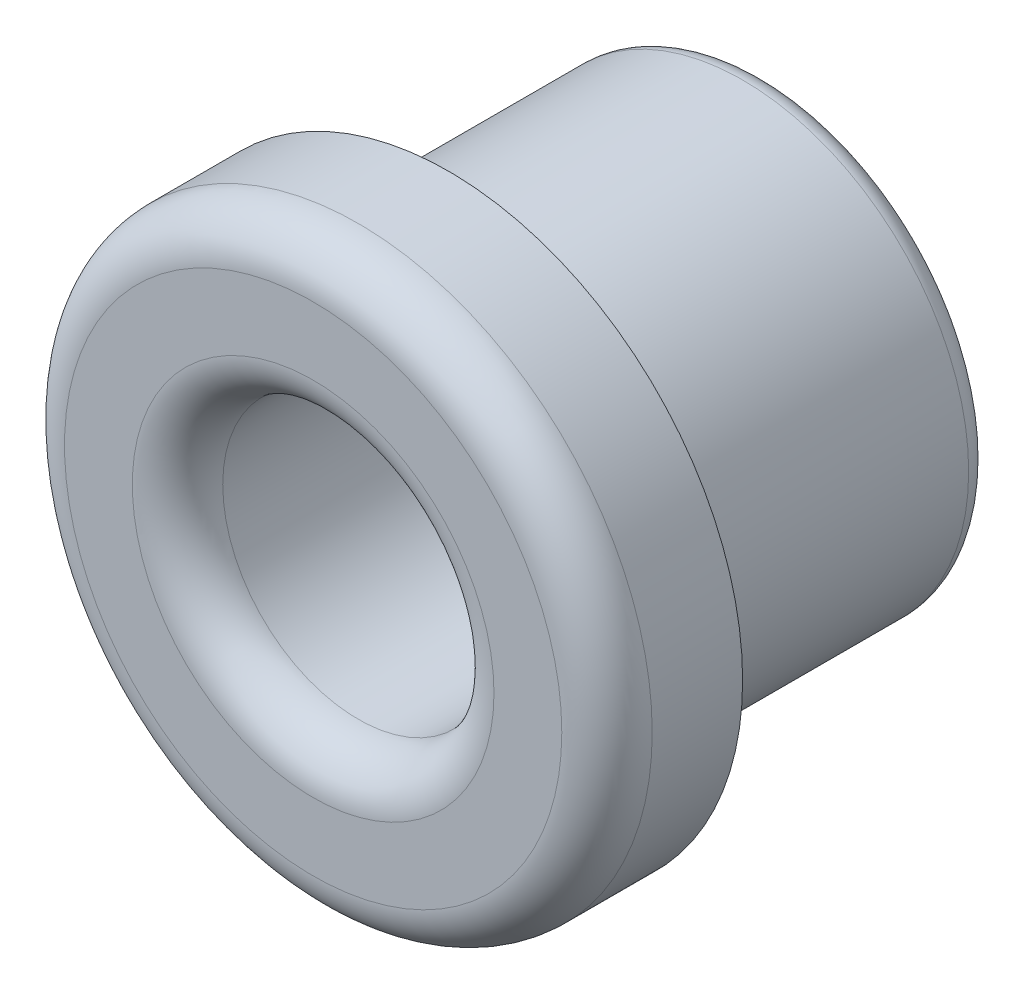
SolidWorks part; units mm, degrees
ref_plane "Front Plane" through (0, 0, 0) normal (0, 0, 1) x (1, 0, 0)
ref_plane "Top Plane" through (0, 0, 0) normal (0, 1, 0) x (1, 0, 0)
ref_plane "Right Plane" through (0, 0, 0) normal (1, 0, 0) x (0, 0, -1)
sketch "Sketch1" plane through (0, 0, 0) normal (0, 0, 1) x (1, 0, 0)
  circle A0 centre (0, 0) radius 5
  circle A1 centre (0, 0) radius 3
  dimension "D1" = 10
  dimension "D2" = 6
extrude "Boss-Extrude1" add sketch "Sketch1" along normal blind 7
sketch "Sketch2" plane through (0, 0, 7) normal (0, 0, 1) x (1, 0, 0)
  circle A0 centre (0, 0) radius 3
  circle A1 centre (0, 0) radius 6.5
  dimension "D1" = 13
extrude "Boss-Extrude2" add sketch "Sketch2" along normal blind 3
fillet "Fillet1" radius 1 2 edges at (3, 0, 10) (6.5, 0, 10)
fillet "Fillet2" radius 0.5 1 edges at (5, 0, 0)
sketch "Sketch3" plane through (0, 0, 0) normal (0, 0, -1) x (-1, 0, 0)
  line L0 (-8.5319, 0) -> (8.9575, 0) construction
  line L1 (0, 9.578) -> (0, -10.9821) construction
ref_plane "Plane1" through (0, 0, 10) normal (0, 0, 1) x (1, 0, 0)
sketch "Sketch4" plane through (0, 0, 10) normal (0, 0, 1) x (1, 0, 0)
  line L0 (-8.3085, -8.3085) -> (0, 0) construction
  line L1 (0, 0) -> (7.0243, 7.0243) construction
  line L2 (-6.877, 7.3253) -> (0, 0) construction
  line L3 (0, 0) -> (7.4944, -7.4944) construction
  line L4 (0, 9.578) -> (0, -10.9821) construction
  line L5 (8.5319, 0) -> (-8.9575, 0) construction
  dimension "D1" = 45
  dimension "D2" = 45
